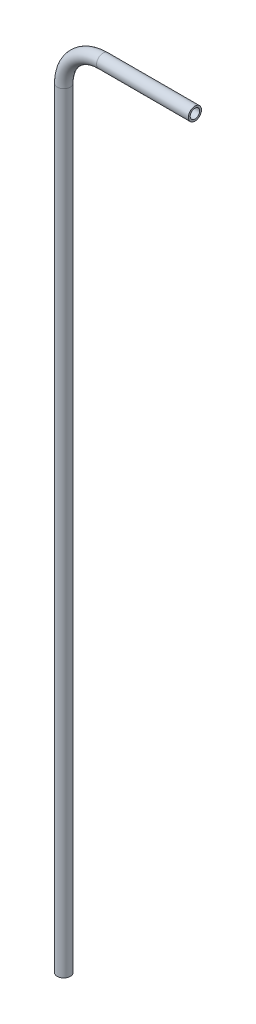
SolidWorks part; units mm, degrees
material "AISI 316 Stainless Steel Sheet (SS)"
ref_plane "Front Plane" through (0, 0, 0) normal (0, 0, 1) x (1, 0, 0)
ref_plane "Top Plane" through (0, 0, 0) normal (0, 1, 0) x (1, 0, 0)
ref_plane "Right Plane" through (0, 0, 0) normal (1, 0, 0) x (0, 0, -1)
sketch "Sketch1" plane through (0, 0, 0) normal (0, 0, 1) x (1, 0, 0)
  line L0 (0, -374.3943) -> (0, -1.5223)
  line L1 (19.05, 17.5277) -> (63.5, 17.5277)
  arc A0 (0, -1.5223) -> (19.05, 17.5277) centre (19.05, -1.5223) cw
  point P6 (0, 17.5277)
  dimension "D3" = 19.05
  dimension "D1" = 63.5
  dimension "D2" = 391.922
ref_plane "Plane1" through (63.5, 17.5277, 0) normal (1, 0, 0) x (0, 0, -1)
sketch "Sketch2" plane through (63.5, 17.5277, 0) normal (1, 0, 0) x (0, 0, -1)
  circle A0 centre (0, 0) radius 3.175
  circle A1 centre (0, 0) radius 2.286
  dimension "D1" = 6.35
  dimension "D2" = 4.572
sweep "Sweep1" add profiles "Sketch2" path "Sketch1"
